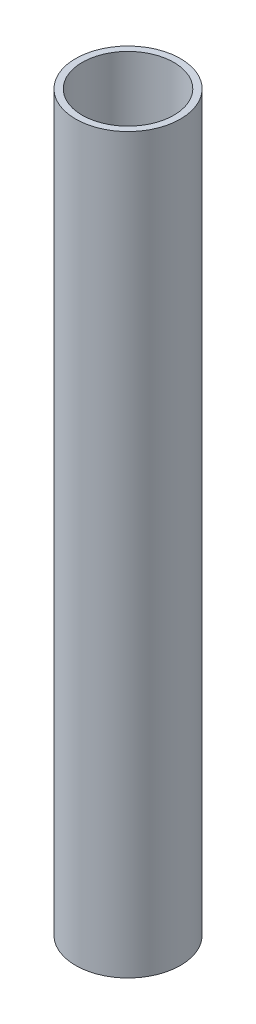
SolidWorks part; units mm, degrees
ref_plane "Front" through (0, 0, 0) normal (0, 0, 1) x (1, 0, 0)
ref_plane "Top" through (0, 0, 0) normal (0, 1, 0) x (1, 0, 0)
ref_plane "Right" through (0, 0, 0) normal (1, 0, 0) x (0, 0, -1)
sketch "Sketch1" plane through (0, 0, 0) normal (0, 1, 0) x (1, 0, 0)
  circle A0 centre (0, 0) radius 38.1
  dimension "D1" = 76.2
extrude "Extrude-Thin1" add sketch "Sketch1" along normal blind 609.6 thin
